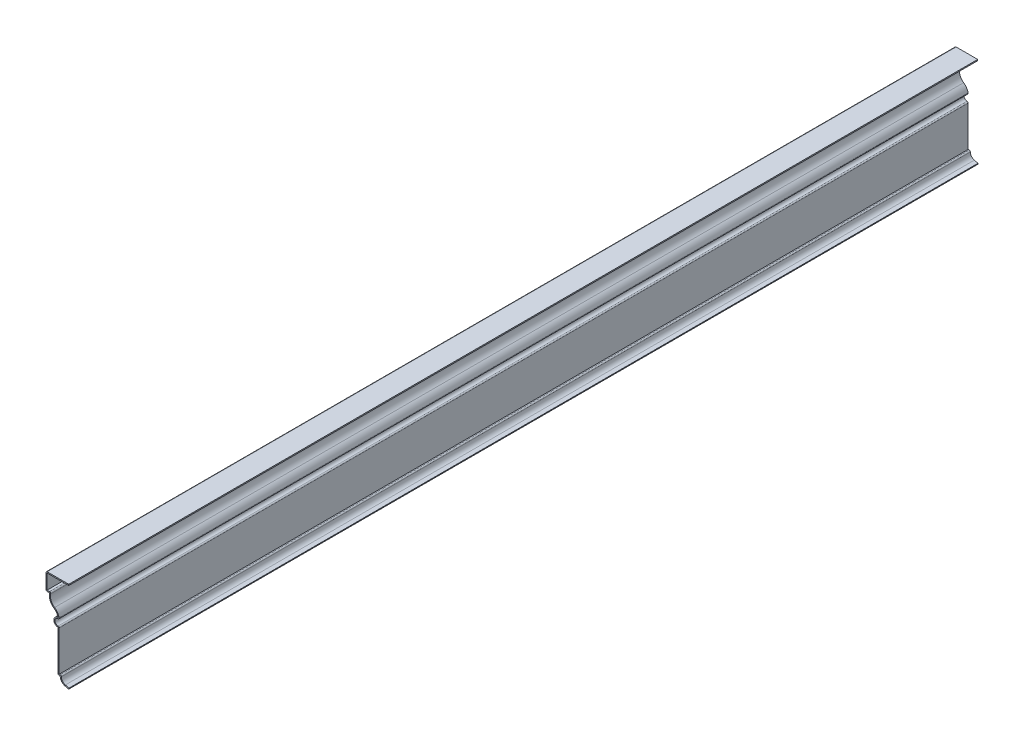
SolidWorks part; units mm, degrees
ref_plane "Front Plane" through (0, 0, 0) normal (0, 0, 1) x (1, 0, 0)
ref_plane "Top Plane" through (0, 0, 0) normal (0, 1, 0) x (1, 0, 0)
ref_plane "Right Plane" through (0, 0, 0) normal (1, 0, 0) x (0, 0, -1)
sketch "Sketch1" plane through (0, 0, 0) normal (0, 0, 1) x (1, 0, 0)
  line L0 (0, 0) -> (-4.0797, 0.9986)
  line L1 (-9.525, 7.9375) -> (-11.9062, 7.9375)
  line L2 (-11.9062, 7.9375) -> (-11.9062, 53.975)
  line L3 (-21.4312, 82.55) -> (-25.4, 82.55)
  line L4 (-25.4, 82.55) -> (-25.4, 101.6)
  line L5 (-25.4, 101.6) -> (0, 101.6)
  line L6 (-11.9062, 63.5) -> (-22.7224, 63.5) construction
  line L7 (-22.7224, 63.5) -> (-22.7224, 60.9508) construction
  line L8 (-21.4312, 82.55) -> (-9.8011, 82.55) construction
  line L9 (-9.8011, 82.55) -> (-9.8011, 80.0008) construction
  arc A0 (-4.0797, 0.9986) -> (-9.525, 7.9375) centre (-2.3813, 7.9375) cw
  arc A1 (-11.9062, 53.975) -> (-11.9062, 63.5) centre (-11.9062, 58.7375) cw
  arc A2 (-11.9062, 63.5) -> (-16.4845, 70.1474) centre (-22.7224, 60.9508) ccw
  arc A3 (-16.4845, 70.1474) -> (-21.4312, 82.55) centre (-9.8011, 80.0008) cw
  dimension "D2" = 11.1125
  dimension "D3" = 11.9062
  dimension "D4" = 7.1437
  dimension "D8" = 4.7625
  dimension "D1" = 101.6
  dimension "D5" = 7.9375
  dimension "D6" = 9.525
  dimension "D7" = 2.3813
  dimension "D9" = 9.525
  dimension "D10" = 46.0375
  dimension "D11" = 19.05
  dimension "D12" = 25.4
  dimension "D13" = 3.9688
extrude "Extrude-Thin1" add sketch "Sketch1" against normal blind 1016 thin
fillet "Fillet1" radius 1.27 7 edges at (-8.1161, 9.2075, -508) (-11.9062, 7.9375, -508) (-10.6363, 55.4841, -508) (-10.3745, 61.8762, -508) (-19.728, 83.82, -508) (-25.4, 82.55, -508) (-25.4, 101.6, -508)
